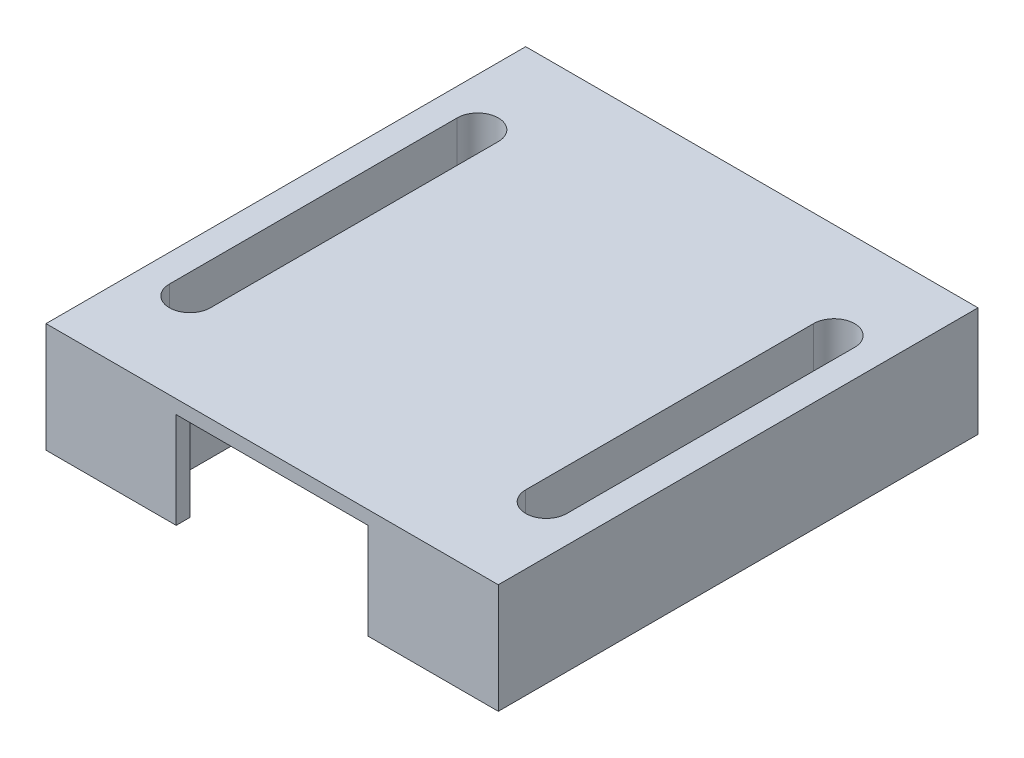
SolidWorks part; units mm, degrees
ref_plane "Front Plane" through (0, 0, 0) normal (0, 0, 1) x (1, 0, 0)
ref_plane "Top Plane" through (0, 0, 0) normal (0, 1, 0) x (1, 0, 0)
ref_plane "Right Plane" through (0, 0, 0) normal (1, 0, 0) x (0, 0, -1)
sketch "Sketch1" plane through (0, 0, 0) normal (0, 1, 0) x (1, 0, 0)
  line L1 (-16.5, -17.5) -> (16.5, -17.5)
  line L2 (-16.5, -17.5) -> (-16.5, 17.5)
  line L3 (-16.5, 17.5) -> (16.5, 17.5)
  line L4 (16.5, -17.5) -> (16.5, 17.5)
  line L5 (0, 17.5) -> (0, -17.5) construction
  line L6 (-16.5, 0) -> (16.5, 0) construction
  point P0 (0, 0)
  dimension "D1" = 33
  dimension "D2" = 35
extrude "Boss-Extrude1" add sketch "Sketch1" along normal blind 8
sketch "Sketch2" plane through (0, 0, 0) normal (0, -1, 0) x (1, 0, 0)
  line L1 (-10, 16.5) -> (10, 16.5)
  line L2 (-10, 16.5) -> (-10, -16.5)
  line L3 (-10, -16.5) -> (10, -16.5)
  line L4 (10, 16.5) -> (10, -16.5)
  line L5 (0, -16.5) -> (0, 16.5) construction
  line L6 (-10, 0) -> (10, 0) construction
  point P0 (0, 0)
  dimension "D1" = 20
  dimension "D2" = 33
extrude "Cut-Extrude1" cut sketch "Sketch2" against normal blind 7
sketch "Sketch3" plane through (0, 0, 17.5) normal (0, 0, 1) x (1, 0, 0)
  line L0 (-16.5, 0) -> (16.5, 0) construction
  line L1 (7, 7) -> (-7, 7)
  line L2 (7, 7) -> (7, 0)
  line L3 (7, 0) -> (-7, 0)
  line L4 (-7, 7) -> (-7, 0)
  line L5 (0, 0) -> (0, 7) construction
  line L6 (7, 3.5) -> (-7, 3.5) construction
  point P0 (0, 3.5)
  point P6 (0, 0)
  point P7 (0, 3.0949)
  dimension "D1" = 7
  dimension "D2" = 14
sketch "Sketch4" plane through (0, 8, 0) normal (0, 1, 0) x (1, 0, 0)
  line L0 (13, 10.5) -> (13, -10.5) construction
  line L1 (14.5, 10.5) -> (14.5, -10.5)
  line L2 (11.5, 10.5) -> (11.5, -10.5)
  line L3 (16.5, -17.5) -> (16.5, 17.5) construction
  line L4 (0, -4.4) -> (0, 4.4) construction
  line L5 (-13, 10.5) -> (-13, -10.5) construction
  line L6 (-14.5, 10.5) -> (-14.5, -10.5)
  line L7 (-11.5, 10.5) -> (-11.5, -10.5)
  arc A0 (14.5, 10.5) -> (11.5, 10.5) centre (13, 10.5) ccw
  arc A1 (11.5, -10.5) -> (14.5, -10.5) centre (13, -10.5) ccw
  arc A2 (-14.5, 10.5) -> (-11.5, 10.5) centre (-13, 10.5) cw
  arc A3 (-11.5, -10.5) -> (-14.5, -10.5) centre (-13, -10.5) cw
  point P2 (13, 0)
  point P7 (0, 0)
  point P11 (13, 12)
  point P12 (13, -12)
  point P17 (-13, 0)
  dimension "D1" = 1.5
  dimension "D2" = 2
  dimension "D3" = 24
extrude "Cut-Extrude3" cut sketch "Sketch4" against normal through all
extrude "Cut-Extrude4" cut sketch "Sketch3" against normal blind 7
